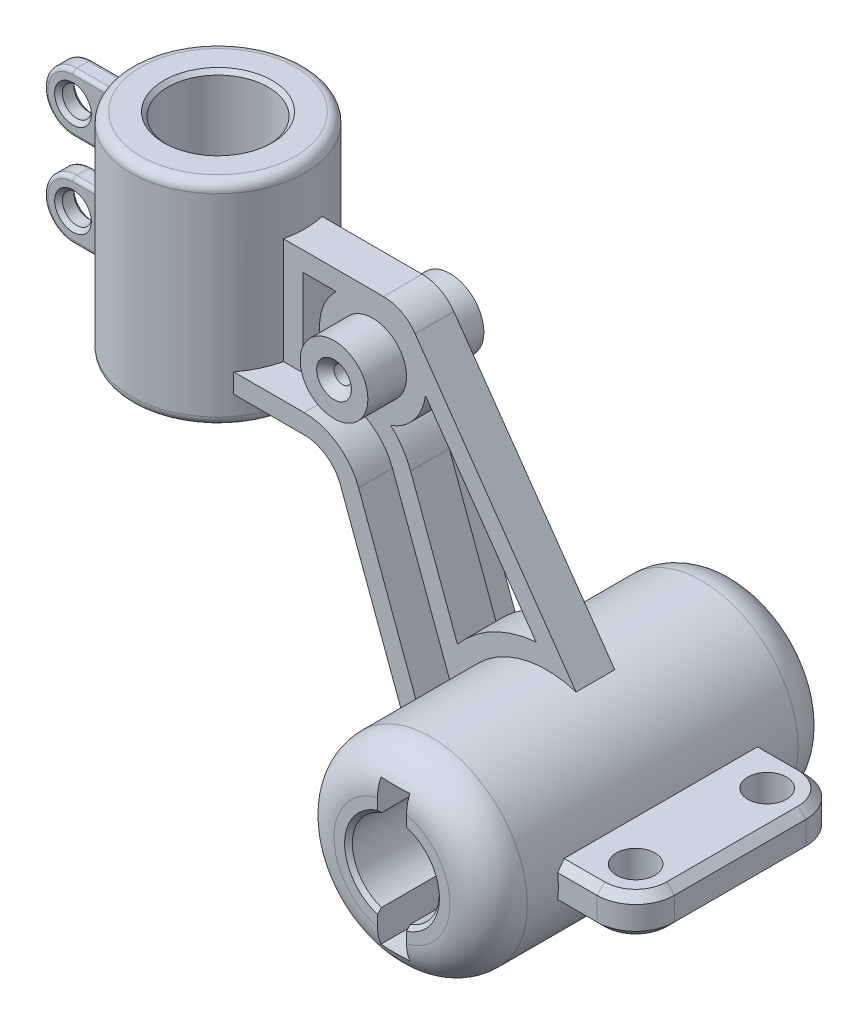
SolidWorks part; units mm, degrees
material "1060 Alloy"
ref_plane "Front Plane" through (0, 0, 0) normal (0, 0, 1) x (1, 0, 0)
ref_plane "Top Plane" through (0, 0, 0) normal (0, 1, 0) x (1, 0, 0)
ref_plane "Right Plane" through (0, 0, 0) normal (1, 0, 0) x (0, 0, -1)
sketch "Sketch1" plane through (0, 0, 0) normal (0, 0, 1) x (1, 0, 0)
  circle A0 centre (0, 0) radius 50
  circle A1 centre (0, 0) radius 22.5
  dimension "D1" = 100
  dimension "D2" = 45
extrude "Boss-Extrude1" add sketch "Sketch1" along normal mid plane 180
fillet "Fillet1" radius 20 2 edges at (50, 0, -90) (50, 0, 90)
sketch "Sketch3" plane through (0, 0, 0) normal (0, 1, 0) x (1, 0, 0)
  circle A0 centre (-180, 0) radius 45
  circle A1 centre (-180, 0) radius 26
  dimension "D1" = 90
  dimension "D2" = 52
  dimension "D3" = 180
extrude "Boss-Extrude2" add sketch "Sketch3" along normal blind 110 from offset 95 separate body
fillet "Fillet2" radius 5 2 edges at (-180, 205, 45) (-180, 95, 45)
sketch "Sketch2" plane through (0, 0, 0) normal (0, 0, 1) x (1, 0, 0)
  line L0 (-46.8946, -17.3463) -> (-94, 110)
  line L1 (-94, 110) -> (-146, 110)
  line L2 (-146, 110) -> (-146, 175)
  line L3 (-146, 175) -> (-74, 175)
  line L4 (-74, 175) -> (15.178, 47.6406)
  line L6 (-220, 95) -> (-140, 95) construction
  arc A0 (15.178, 47.6406) -> (-46.8946, -17.3463) centre (0, 0) ccw
  circle A1 centre (0, 0) radius 50 construction
  dimension "D1" = 125
  dimension "D2" = 15
  dimension "D3" = 80
  dimension "D4" = 60
  dimension "D5" = 80
  dimension "D6" = 72
extrude "Boss-Extrude3" add sketch "Sketch2" along normal mid plane 20
fillet "Fillet3" radius 20 2 edges at (-94, 110, 0) (-74, 175, 0)
sketch "Sketch5" plane through (0, 0, 0) normal (0, 0, 1) x (1, 0, 0)
  line L0 (-89.1686, 96.9385) -> (-46.8946, -17.3463) construction
  line L1 (-136.1252, 110) -> (-107.9264, 110) construction
  line L2 (-89.1686, 96.9385) -> (-46.8946, -17.3463)
  line L3 (-136.1252, 110) -> (-107.9264, 110)
  line L4 (-136.1252, 120) -> (-107.9264, 120)
  line L5 (-79.7896, 100.4078) -> (-37.5157, -13.877)
  line L7 (-46.8946, -17.3463) -> (-37.5157, -13.877)
  line L8 (-136.1252, 110) -> (-148.1252, 110)
  line L9 (-148.1252, 110) -> (-148.1252, 120)
  line L10 (-148.1252, 120) -> (-136.1252, 120)
  arc A0 (-89.1686, 96.9385) -> (-107.9264, 110) centre (-107.9264, 90) ccw construction
  arc A1 (-89.1686, 96.9385) -> (-107.9264, 110) centre (-107.9264, 90) ccw
  arc A2 (-79.7896, 100.4078) -> (-107.9264, 120) centre (-107.9264, 90) ccw
  dimension "D2" = 12
  dimension "D1" = 10
extrude "Boss-Extrude5" add sketch "Sketch5" along normal mid plane 55
chamfer "Chamfer1" distance 2 angle 45 4 edges at (22.5, 0, -90) (22.5, 0, 90) (-180, 95, 26) (-180, 205, 26)
sketch "Sketch6" plane through (0, 0, -90) normal (0, 0, -1) x (-1, 0, 0)
  line L1 (7.5, -37.5) -> (-7.5, -37.5)
  line L2 (7.5, -37.5) -> (7.5, 37.5)
  line L3 (7.5, 37.5) -> (-7.5, 37.5)
  line L4 (-7.5, -37.5) -> (-7.5, 37.5)
  line L5 (7.5, -37.5) -> (-7.5, 37.5) construction
  line L6 (7.5, 37.5) -> (-7.5, -37.5) construction
  point P0 (0, 0)
  dimension "D1" = 15
  dimension "D2" = 75
extrude "Cut-Extrude1" cut sketch "Sketch6" against normal through all both and the other way through all
sketch "Sketch7" plane through (0, 0, 10) normal (0, 0, 1) x (1, 0, 0)
  line L0 (-5.5066, 59.7468) -> (-62.7279, 141.4672)
  line L2 (-79.7896, 100.4078) -> (-47.9235, 14.2597) construction
  line L4 (15.178, 47.6406) -> (-68.0283, 166.4715) construction
  line L5 (-220, 95) -> (-140, 95) construction
  line L10 (-46.1636, 38.3265) -> (-70.4107, 103.877)
  arc A0 (-46.1636, 38.3265) -> (-5.5066, 59.7468) centre (0, 0) cw
  arc A1 (-80.5583, 119.1716) -> (-62.7279, 141.4672) centre (-90, 145) ccw
  arc A2 (-79.7896, 100.4078) -> (-107.9264, 120) centre (-107.9264, 90) ccw construction
  arc A3 (-79.7896, 100.4078) -> (-107.9264, 120) centre (-107.9264, 90) ccw construction
  arc A5 (-70.4107, 103.877) -> (-80.5583, 119.1716) centre (-107.9264, 90) ccw
  point P15 (-180, 95)
  dimension "D1" = 60
  dimension "D5" = 10
  dimension "D6" = 27.5
  dimension "D2" = 10
  dimension "D3" = 90
  dimension "D4" = 50
  dimension "D7" = 10
extrude "Cut-Extrude2" cut sketch "Sketch7" against normal through all both
sketch "Sketch8" plane through (0, 0, 10) normal (0, 0, 1) x (1, 0, 0)
  line L3 (-108.8746, 165) -> (-126.1252, 165)
  line L4 (-126.1252, 165) -> (-126.1252, 130)
  line L5 (-126.1252, 130) -> (-113.0489, 130)
  line L6 (-84.4113, 175) -> (-136.1252, 175) construction
  line L7 (-107.9264, 120) -> (-144.3805, 120) construction
  line L8 (-136.1252, 175) -> (-136.1252, 120) construction
  arc A1 (-108.8746, 165) -> (-113.0489, 130) centre (-90, 145) ccw
  arc A2 (-80.5583, 119.1716) -> (-62.7279, 141.4672) centre (-90, 145) ccw construction
  dimension "D1" = 27.5
  dimension "D2" = 10
  dimension "D3" = 10
  dimension "D4" = 10
extrude "Cut-Extrude3" cut sketch "Sketch8" against normal through all both
sketch "Sketch9" plane through (0, 0, 0) normal (0, 0, 1) x (1, 0, 0)
  circle A0 centre (-90, 145) radius 17.5
  arc A1 (-108.8746, 165) -> (-113.0489, 130) centre (-90, 145) ccw construction
  dimension "D1" = 35
extrude "Boss-Extrude6" add sketch "Sketch9" along normal mid plane 60
hole_wizard "CSK for M8 Hex Socket Countersunk Cap Screw1" positions "Sketch10" profile "Sketch11" countersink size "M8" standard "ISO" end condition through all
sketch "Sketch10" plane through (0, 0, 30) normal (0, 0, 1) x (1, 0, 0)
  circle A0 centre (-90, 145) radius 17.5 construction
  point P0 (-90, 145)
sketch "Sketch11" plane through (-90, 145, 30) normal (1, 0, 0) x (0, -1, 0)
  line L0 (0, 0) -> (0, 121.2998)
  line L1 (0, 121.2998) -> (4.5, 121.2998)
  line L2 (4.5, 121.2998) -> (4.5, 4.46)
  line L3 (4.5, 4.46) -> (8.96, 0)
  line L5 (8.96, 0) -> (0, 0)
  line L6 (-4.5, 4.46) -> (-8.96, 0) construction
  line L11 (0, -6.35) -> (0, 107.95) construction
  dimension "Thru Hole Dia." = 9
  dimension "Thru Hole Depth" = 121.2998
  dimension "Near C'Sink Dia." = 17.92
  dimension "Near C'Sink Angle" = 90
sketch "Sketch13" plane through (0, 0, 0) normal (0, 0, 1) x (1, 0, 0)
  line L0 (-67.0808, 37.2258) -> (-128.1457, 110)
  line L1 (-89.1686, 96.9385) -> (-46.8946, -17.3463) construction
  line L2 (-144.3805, 110) -> (-107.9264, 110) construction
  line L3 (-119.6347, 110) -> (81.63, 110) construction
  dimension "D1" = 95
  dimension "D2" = 50
rib "Rib1" sketch "Sketch13" sketch "Sketch13" thickness 10 extrusion direction parallel to sketch draft on no parameters "D1"=10
sketch "Sketch14" plane through (0, 0, 0) normal (0, 1, 0) x (1, 0, 0)
  line L6 (70, -54) -> (40, -54)
  line L7 (90, -34) -> (90, 34)
  line L8 (70, 54) -> (40, 54)
  line L10 (90, -54) -> (40, 54) construction
  line L11 (90, 54) -> (40, -54) construction
  line L12 (40, 54) -> (40, -54)
  line L13 (50, -70) -> (50, 70) construction
  arc A0 (90, 34) -> (70, 54) centre (70, 34) ccw
  arc A1 (70, -54) -> (90, -34) centre (70, -34) ccw
  circle A2 centre (70, 34) radius 10
  circle A3 centre (70, -34) radius 10
  point P0 (65, 0)
  dimension "D3" = 20
  dimension "D4" = 20
  dimension "D1" = 108
  dimension "D2" = 90
  dimension "D5" = 10
extrude "Boss-Extrude8" add sketch "Sketch14" along normal mid plane 20
chamfer "Chamfer2" distance 4 angle 45 10 edges at (59.4949, -10, 54) (59.4949, -10, -54) (84.1421, -10, 48.1421) (84.1421, -10, -48.1421) (90, -10, 0) (59.4949, 10, 54) (59.4949, 10, -54) (84.1421, 10, 48.1421) (84.1421, 10, -48.1421) (90, 10, 0)
sketch "Sketch15" plane through (0, 0, 0) normal (0, 0, 1) x (1, 0, 0)
  line L0 (-217.5, 143) -> (-217.5, 113)
  line L1 (-217.5, 113) -> (-250, 113)
  line L2 (-217.5, 143) -> (-250, 143)
  line L3 (-180, 95) -> (-180, 258.4468) construction
  line L4 (-220, 95) -> (-140, 95) construction
  line L5 (-225, 200) -> (-225, 100) construction
  line L6 (-217.5, 161) -> (-250, 161)
  line L7 (-217.5, 191) -> (-217.5, 161)
  line L8 (-217.5, 191) -> (-250, 191)
  arc A0 (-250, 143) -> (-250, 113) centre (-250, 128) ccw
  arc A1 (-250, 191) -> (-250, 161) centre (-250, 176) ccw
  circle A2 centre (-250, 176) radius 7.5
  circle A3 centre (-250, 128) radius 7.5
  dimension "D7" = 15
  dimension "D1" = 30
  dimension "D2" = 70
  dimension "D3" = 18
  dimension "D4" = 7.5
  dimension "D6" = 18
  dimension "D5" = 2
extrude "Boss-Extrude9" add sketch "Sketch15" along normal mid plane 10
fillet "Fillet4" radius 2 20 edges at (-224.7214, 176, -5) (-224.7214, 128, -5) (-225, 113, 0) (-225, 191, 0) (-225, 161, 0) (-225, 143, 0) (-237.3607, 113, -5) (-265, 128, -5) (-237.3607, 113, 5) (-265, 128, 5) (-237.3607, 161, -5) (-265, 176, -5) (-237.3607, 191, 5) (-237.3607, 161, 5) (-224.7214, 128, 5) (-224.7214, 176, 5) (-237.3607, 143, -5) (-237.3607, 143, 5) (-237.3607, 191, -5) (-265, 176, 5)
chamfer "Chamfer3" distance 2 angle 45 4 edges at (-242.5, 128, -5) (-242.5, 176, -5) (-242.5, 128, 5) (-242.5, 176, 5)
equation "\"A\"= 90"
equation "\"B\"= 180"
equation "\"C\"= 100"
equation "\"D\"= 110"
equation "\"E\"= \"A\" / 2 + 10"
equation "\"Y\"= \"A\" * 1.2"
equation "\"D1@Sketch1\"=\"C\""
equation "\"D1@Boss-Extrude1\"=\"B\""
equation "\"D1@Sketch3\"=\"A\""
equation "\"D3@Sketch3\"=\"B\""
equation "\"D1@Boss-Extrude2\"=\"D\""
equation "\"D1@Boss-Extrude5\"=\"E\""
equation "\"X\"= 95"
equation "\"D1@Sketch13\"=\"X\""
equation "\"D1@Sketch14\"=\"Y\""
